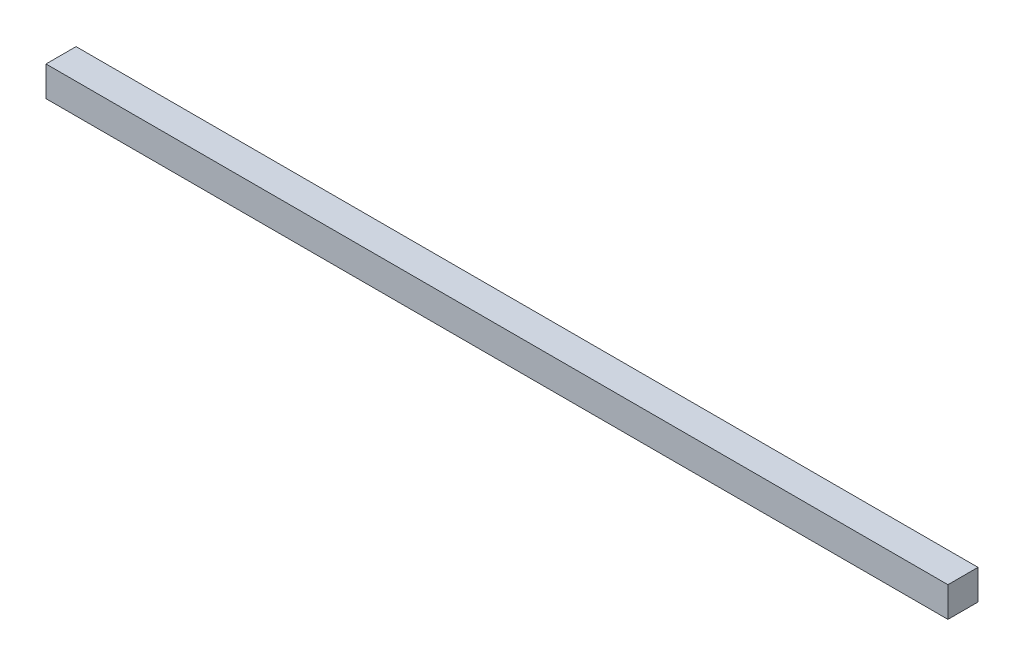
SolidWorks part; units mm, degrees
ref_plane "Plan de face" through (0, 0, 0) normal (0, 0, 1) x (1, 0, 0)
ref_plane "Plan de dessus" through (0, 0, 0) normal (0, 1, 0) x (1, 0, 0)
ref_plane "Plan de droite" through (0, 0, 0) normal (1, 0, 0) x (0, 0, -1)
sketch "Esquisse1" plane through (0, 0, 0) normal (0, 0, 1) x (1, 0, 0)
  line L1 (-63.0667, 10.7996) -> (236.9333, 10.7996)
  line L2 (-63.0667, 10.7996) -> (-63.0667, 0.7996)
  line L3 (-63.0667, 0.7996) -> (236.9333, 0.7996)
  line L4 (236.9333, 10.7996) -> (236.9333, 0.7996)
extrude "Boss.-Extru.1" add sketch "Esquisse1" along normal blind 10
